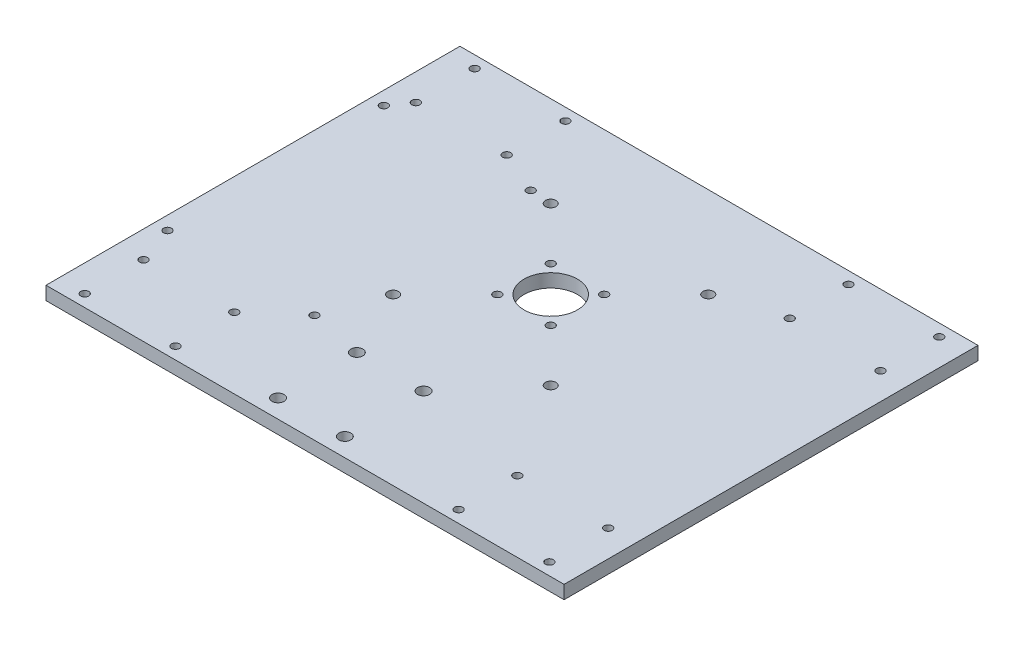
SolidWorks part; units mm, degrees
ref_plane "Front Plane" through (0, 0, 0) normal (0, 0, 1) x (1, 0, 0)
ref_plane "Top Plane" through (0, 0, 0) normal (0, 1, 0) x (1, 0, 0)
ref_plane "Right Plane" through (0, 0, 0) normal (1, 0, 0) x (0, 0, -1)
sketch "Sketch1" plane through (0, 0, 0) normal (0, 1, 0) x (1, 0, 0)
  line L1 (0, 0) -> (194, 0)
  line L2 (0, 0) -> (0, 155)
  line L3 (0, 155) -> (194, 155)
  line L4 (194, 0) -> (194, 155)
  dimension "D1" = 155
  dimension "D2" = 194
extrude "Boss-Extrude1" add sketch "Sketch1" along normal blind 5
sketch "Sketch2" plane through (0, 5, 0) normal (0, 1, 0) x (1, 0, 0)
  line L0 (194, 155) -> (0, 155) construction
  line L1 (0, 0) -> (194, 0) construction
  line L2 (68, 60) -> (68, 64) construction
  line L3 (127, 123) -> (127, 119) construction
  line L4 (70, 62) -> (66, 62) construction
  line L5 (125, 121) -> (129, 121) construction
  line L6 (68, 60) -> (68, 170.8676) construction
  circle A0 centre (68, 121) radius 2
  circle A1 centre (127, 121) radius 2
  circle A2 centre (68, 62) radius 2
  circle A3 centre (127, 62) radius 2
  point P4 (97, 155)
  dimension "D4" = 4
  dimension "D1" = 59
  dimension "D2" = 29
  dimension "D6" = 62
  dimension "D7" = 59
  dimension "D3" = 2
extrude "Cut-Extrude1" cut sketch "Sketch2" against normal through all
sketch "Sketch3" plane through (0, 5, 0) normal (0, 1, 0) x (1, 0, 0)
  circle A0 centre (97.5, 91.5) radius 10
  circle A1 centre (68, 121) radius 2 construction
  circle A3 centre (68, 121) radius 2 construction
  circle A4 centre (107.5, 101.5) radius 1.5
  circle A6 centre (107.5, 81.5) radius 1.5
  circle A8 centre (87.5, 81.5) radius 1.5
  circle A10 centre (87.5, 101.5) radius 1.5
  dimension "D3" = 20
  dimension "D5" = 10
  dimension "D4" = 20
  dimension "D8" = 3
  dimension "D1" = 29.5
  dimension "D2" = 29.5
  dimension "D6" = 10
  dimension "D7" = 10
extrude "Cut-Extrude2" cut sketch "Sketch3" against normal through all
sketch "Sketch4" plane through (0, 0, 0) normal (0, -1, 0) x (-1, 0, 0)
  line L0 (0, 155) -> (0, 0) construction
  circle A0 centre (-80, 6.8964) radius 2.25
  circle A1 centre (-105, 6.8964) radius 2.25
  circle A2 centre (-80, 36.3964) radius 2.25
  circle A3 centre (-105, 36.3964) radius 2.25
  dimension "D1" = 4.5
  dimension "D2" = 80
  dimension "D3" = 29.5
  dimension "D4" = 25
extrude "Cut-Extrude3" cut sketch "Sketch4" against normal through all
sketch "Sketch5" plane through (0, 5, 0) normal (0, 1, 0) x (1, 0, 0)
  line L0 (0, 0) -> (194, 0) construction
  line L1 (0, 155) -> (0, 0) construction
  line L2 (194, 0) -> (194, 155) construction
  line L3 (194, 155) -> (0, 155) construction
  circle A0 centre (10, 4.5) radius 1.5
  circle A1 centre (44, 4.5) radius 1.5
  circle A2 centre (44, 26.5) radius 1.5
  circle A3 centre (10, 26.5) radius 1.5
  circle A4 centre (150, 4.5) radius 1.5
  circle A5 centre (150, 26.5) radius 1.5
  circle A6 centre (184, 26.5) radius 1.5
  circle A7 centre (184, 4.5) radius 1.5
  circle A8 centre (150, 128.5) radius 1.5
  circle A9 centre (150, 150.5) radius 1.5
  circle A10 centre (184, 150.5) radius 1.5
  circle A11 centre (184, 128.5) radius 1.5
  circle A12 centre (10, 128.5) radius 1.5
  circle A13 centre (10, 150.5) radius 1.5
  circle A14 centre (44, 150.5) radius 1.5
  circle A15 centre (44, 128.5) radius 1.5
  dimension "D1" = 3
  dimension "D2" = 4.5
  dimension "D3" = 10
  dimension "D4" = 34
  dimension "D5" = 22
  dimension "D8" = 10
  dimension "D9" = 4.5
  dimension "D10" = 10
  dimension "D11" = 4.5
  dimension "D6" = 2
  dimension "D7" = 2
extrude "Cut-Extrude4" cut sketch "Sketch5" against normal through all
sketch "Sketch6" plane through (0, 5, 0) normal (0, 1, 0) x (1, 0, 0)
  line L0 (0, 155) -> (0, 0) construction
  line L1 (194, 155) -> (0, 155) construction
  circle A0 centre (5, 121.5) radius 1.5
  circle A1 centre (60, 121.5) radius 1.5
  circle A2 centre (5, 40.5) radius 1.5
  circle A3 centre (60, 40.5) radius 1.5
  dimension "D1" = 3
  dimension "D2" = 5
  dimension "D3" = 33.5
  dimension "D4" = 55
  dimension "D5" = 81
extrude "Cut-Extrude5" cut sketch "Sketch6" against normal through all
